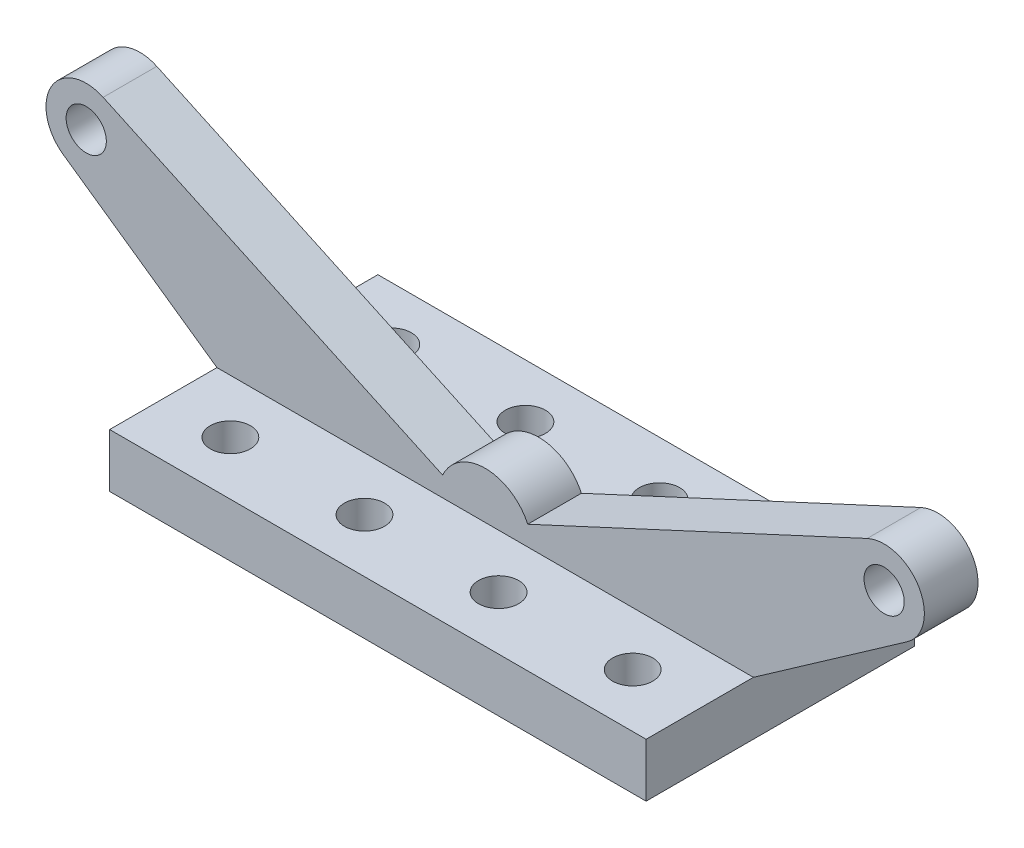
SolidWorks part; units mm, degrees
ref_plane "Front Plane" through (0, 0, 0) normal (0, 0, 1) x (1, 0, 0)
ref_plane "Top Plane" through (0, 0, 0) normal (0, 1, 0) x (1, 0, 0)
ref_plane "Right Plane" through (0, 0, 0) normal (1, 0, 0) x (0, 0, -1)
sketch "Sketch1" plane through (0, 0, 0) normal (0, 1, 0) x (1, 0, 0)
  line L1 (-100, 50) -> (100, 50)
  line L2 (-100, 50) -> (-100, -50)
  line L3 (-100, -50) -> (100, -50)
  line L4 (100, 50) -> (100, -50)
  line L5 (-100, 50) -> (100, -50) construction
  line L6 (-100, -50) -> (100, 50) construction
  point P0 (0, 0)
  dimension "D1" = 200
  dimension "D2" = 100
extrude "Boss-Extrude1" add sketch "Sketch1" along normal blind 20
sketch "Sketch2" plane through (0, 20, 0) normal (0, 1, 0) x (1, 0, 0)
  line L0 (-100, 50) -> (-100, -50) construction
  line L1 (100, 50) -> (-100, 50) construction
  circle A0 centre (-75, 30) radius 7.5
  circle A1 centre (-25, 30) radius 7.5
  circle A2 centre (25, 30) radius 7.5
  circle A3 centre (75, 30) radius 7.5
  circle A4 centre (-75, -30) radius 7.5
  circle A5 centre (-25, -30) radius 7.5
  circle A6 centre (25, -30) radius 7.5
  circle A7 centre (75, -30) radius 7.5
  dimension "D1" = 15
  dimension "D2" = 25
  dimension "D3" = 20
  dimension "D4" = 4
  dimension "D5" = 2
extrude "Cut-Extrude1" cut sketch "Sketch2" against normal blind 20
ref_plane "Plane1" through (0, 0, 0) normal (0, 0, 1) x (1, 0, 0)
sketch "Sketch3" plane through (0, 0, 0) normal (0, 0, 1) x (1, 0, 0)
  line L0 (-100, 20) -> (100, 20)
  line L1 (100, 20) -> (157.3406, 60.1504)
  line L2 (-100, 20) -> (-157.3406, 60.1504)
  line L3 (142.4267, 86.0457) -> (15.8761, 27.362)
  line L4 (-142.4267, 86.0457) -> (-15.8761, 27.362)
  arc A0 (15.8761, 27.362) -> (-15.8761, 27.362) centre (0, 20) ccw
  arc A1 (157.3406, 60.1504) -> (142.4267, 86.0457) centre (148.737, 72.4376) ccw
  arc A2 (-157.3406, 60.1504) -> (-142.4267, 86.0457) centre (-148.737, 72.4376) cw
  dimension "D5" = 35
  dimension "D6" = 15
  dimension "D7" = 15
  dimension "D1" = 70
  dimension "D2" = 70
  dimension "D3" = 145
  dimension "D4" = 145
extrude "Boss-Extrude2" add sketch "Sketch3" along normal mid plane 20
sketch "Sketch4" plane through (0, 0, 10) normal (0, 0, 1) x (1, 0, 0)
  circle A0 centre (148.737, 72.4376) radius 7.5
  circle A1 centre (-148.737, 72.4376) radius 7.5
  dimension "D1" = 15
  dimension "D2" = 15
extrude "Cut-Extrude2" cut sketch "Sketch4" against normal blind 20
